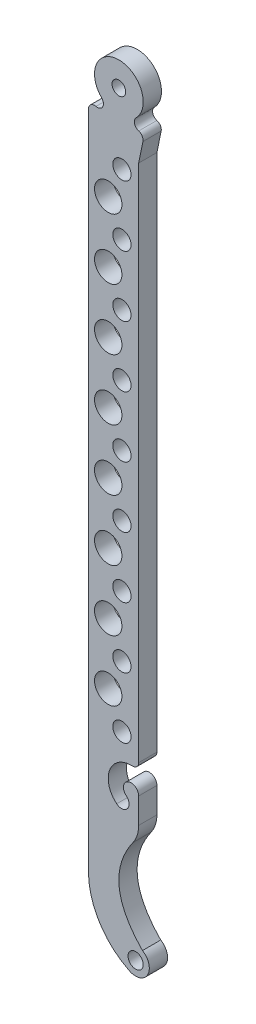
SolidWorks part; units mm, degrees
material "Сплав 2024"
ref_plane "Спереди" through (0, 0, 0) normal (0, 0, 1) x (1, 0, 0)
ref_plane "Сверху" through (0, 0, 0) normal (0, 1, 0) x (1, 0, 0)
ref_plane "Справа" through (0, 0, 0) normal (1, 0, 0) x (0, 0, -1)
sketch "Эскиз1" plane through (0, 0, 0) normal (0, 0, 1) x (1, 0, 0)
  line L0 (0, 19.9837) -> (0, -254.7255) construction
  line L1 (-29.97, -250) -> (36.7046, -250) construction
  line L2 (10, 23.4276) -> (10, -280.6569) construction
  line L3 (5.5, -245.5) -> (2.9019, -250) construction
  line L4 (6.5, -18.1328) -> (6.5, -210)
  line L5 (6.5, -18.1328) -> (9.7974, -2.0028)
  line L6 (10, -237.7058) -> (5.5, -245.5) construction
  line L8 (-10, -227.9756) -> (-10, 0)
  arc A0 (9.7974, -2.0028) -> (-10, 0) centre (0, 0) ccw
  arc A1 (3.25, -249.3971) -> (7.75, -241.6029) centre (5.5, -245.5) ccw
  circle A2 centre (5.5, -245.5) radius 2.5
  circle A3 centre (11, -226) radius 11 construction
  arc A4 (-10, -227.9756) -> (3.25, -249.3971) centre (13.9413, -227.9756) ccw
  spline S0 degree 2 poles (7.75, -241.6029) (-7.1198, -226.3368) (6.5, -210) knots 0 0 0 1 1 1
  dimension "D1" = 20
  dimension "D3" = 5
  dimension "D4" = 9
  dimension "D5" = 22
  dimension "D2" = 250
  dimension "D6" = 40
  dimension "D7" = 3.5
  dimension "D8" = 24
  dimension "D9" = 30
extrude "Бобышка-Вытянуть1" add sketch "Эскиз1" along normal blind 6
sketch "Эскиз2" plane through (0, 0, 6) normal (0, 0, 1) x (1, 0, 0)
  line L0 (6.5, -198.2304) -> (6.5, -191.1593)
  line L1 (6.5, -210) -> (6.5, -18.1328) construction
  arc A0 (6.5, -198.2304) -> (2.4273, -200.1737) centre (4, -198.2304) ccw
  arc A1 (6.5, -191.1593) -> (-0.7182, -204.0604) centre (4, -198.2304) ccw
  arc A2 (-0.7182, -204.0604) -> (2.4273, -200.1737) centre (0.8545, -202.1171) ccw
  dimension "D1" = 5
  dimension "D2" = 15
  dimension "D3" = 5
extrude "Вырез-Вытянуть1" cut sketch "Эскиз2" against normal through all
hole_wizard "Отверстие с зазором M41" positions "Эскиз5" profile "Эскиз4" hole size "M4" standard "Ansi Metric" end condition through all
sketch "Эскиз5" plane through (0, 0, 6) normal (0, 0, 1) x (1, 0, 0)
  point P0 (0, 0)
sketch "Эскиз4" plane through (0, 0, 6) normal (1, 0, 0) x (0, -1, 0)
  line L0 (0, 0) -> (0, 6)
  line L1 (0, 6) -> (2.25, 6)
  line L2 (2.25, 6) -> (2.25, 0)
  line L5 (2.25, 0) -> (0, 0)
  line L11 (0, -6.35) -> (0, 107.95) construction
  dimension "Диаметр сквозного отверстия" = 4.5
  dimension "Глубина сквозного отверстия" = 6
sketch "Эскиз6" plane through (0, 0, 6) normal (0, 0, 1) x (1, 0, 0)
  line L0 (7.0711, 7.0711) -> (-13.6105, -13.6105) construction
  line L1 (-7.3609, 7.3609) -> (9.1645, -9.1645) construction
  line L2 (-10, 0) -> (-10, -227.9756) construction
  arc A0 (9.7974, -2.0028) -> (-10, 0) centre (0, 0) ccw construction
  arc A1 (5.6569, -5.6569) -> (-5.6569, -5.6569) centre (0, 0) ccw
  arc A2 (8.4853, -8.4853) -> (-8.4853, -8.4853) centre (0, 0) ccw
  arc A3 (-8.4853, -8.4853) -> (-5.6569, -5.6569) centre (-7.0711, -7.0711) ccw
  arc A4 (5.6569, -5.6569) -> (8.4853, -8.4853) centre (7.0711, -7.0711) ccw
  circle A6 centre (0, 0) radius 8 construction
  circle A7 centre (0, 0) radius 12 construction
  point P8 (7.1723, 2.1928)
  point P17 (3.3471, 1.0233)
  dimension "D2" = 12
  dimension "D3" = 45
  dimension "D1" = 4
extrude "Вырез-Вытянуть2" cut sketch "Эскиз6" against normal through all
fillet "Скругление1" radius 2 2 edges at (8.4689, -8.5015, 3) (-10, -6.6332, 3)
sketch "Эскиз9" plane through (0, 0, 6) normal (0, 0, 1) x (1, 0, 0)
  line L0 (1, -15.9204) -> (1, -196.7254) construction
  line L1 (-3.5, -15.9204) -> (-3.5, -196.7254) construction
  line L5 (6.5, -191.1593) -> (6.5, -18.1328) construction
  line L6 (-10, -10.9617) -> (-10, -227.9756) construction
  circle A0 centre (1, -22.6728) radius 3
  circle A1 centre (1, -42.6728) radius 3
  circle A2 centre (1, -62.6728) radius 3
  circle A3 centre (1, -82.6728) radius 3
  circle A4 centre (1, -102.6728) radius 3
  circle A5 centre (1, -122.6728) radius 3
  circle A6 centre (1, -142.6728) radius 3
  circle A7 centre (1, -162.6728) radius 3
  circle A8 centre (1, -182.6728) radius 3
  circle A9 centre (-3.5, -32.6728) radius 4.5
  circle A10 centre (-3.5, -52.6728) radius 4.5
  circle A11 centre (-3.5, -72.6728) radius 4.5
  circle A12 centre (-3.5, -92.6728) radius 4.5
  circle A13 centre (-3.5, -112.6728) radius 4.5
  circle A14 centre (-3.5, -132.6728) radius 4.5
  circle A15 centre (-3.5, -152.6728) radius 4.5
  circle A16 centre (-3.5, -172.6728) radius 4.5
  dimension "D3" = 6
  dimension "D5" = 9
  dimension "D1" = 5.5
  dimension "D2" = 6.5
  dimension "D6" = 10
  dimension "D4" = 9
  dimension "D7" = 8
extrude "Вырез-Вытянуть4" cut sketch "Эскиз9" against normal through all
fillet "Скругление4" radius 2 1 edges at (6.5, -191.1593, 3)
fillet "Скругление5" radius 10 1 edges at (6.5, -210, 3)
